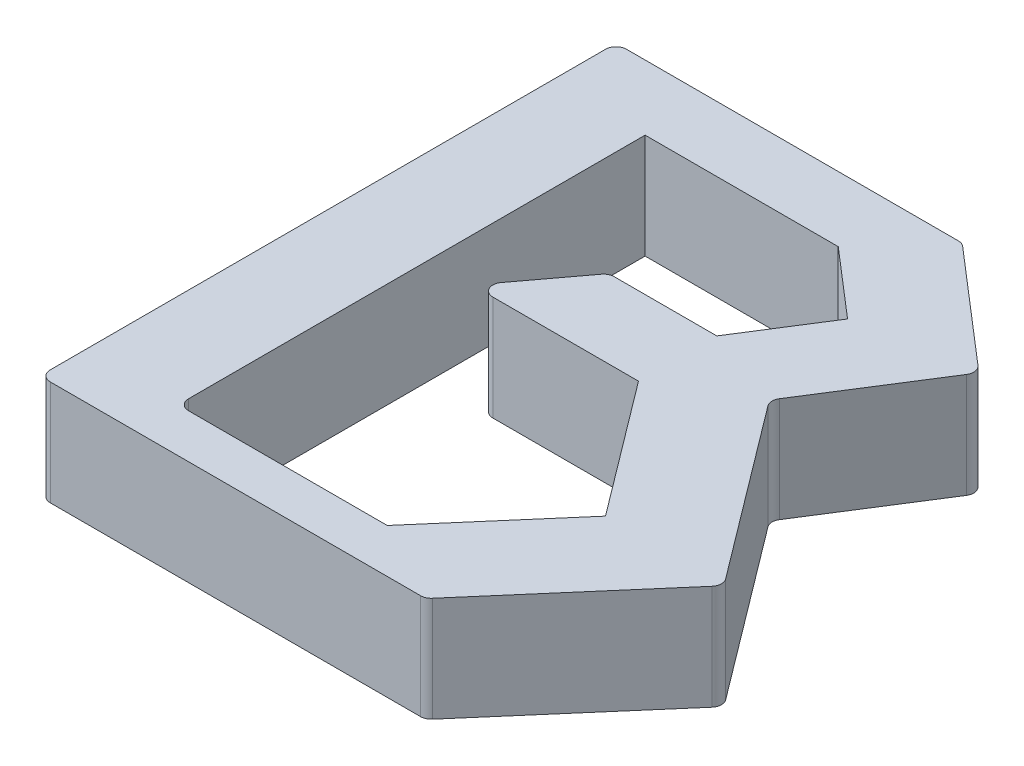
SolidWorks part; units mm, degrees
ref_plane "Front Plane" through (0, 0, 0) normal (0, 0, 1) x (1, 0, 0)
ref_plane "Top Plane" through (0, 0, 0) normal (0, 1, 0) x (1, 0, 0)
ref_plane "Right Plane" through (0, 0, 0) normal (1, 0, 0) x (0, 0, -1)
sketch "Sketch1" plane through (0, 0, 0) normal (0, 1, 0) x (1, 0, 0)
  line L0 (33.0444, 55) -> (44.5679, 45.0706)
  line L1 (0, 0) -> (36.8145, 0)
  line L2 (0, 0) -> (0, 55)
  line L3 (0, 55) -> (33.0444, 55)
  line L6 (44.5679, 45.0706) -> (36.8145, 32.8226)
  line L7 (36.8145, 32.8226) -> (50, 15.3024)
  line L8 (50, 15.3024) -> (36.8145, 0)
  line L9 (8.9879, 48.7885) -> (8.9879, 4.2137)
  line L10 (8.9879, 48.7885) -> (27.4217, 48.7885)
  line L11 (27.4217, 48.7885) -> (33.845, 43.2538)
  line L12 (33.845, 43.2538) -> (29.0072, 35.6117)
  line L13 (29.0072, 35.6117) -> (18.705, 35.6117)
  line L15 (13.1098, 28.136) -> (29.0072, 28.136)
  line L16 (29.0072, 28.136) -> (38.5895, 15.4036)
  line L17 (38.5895, 15.4036) -> (28.9476, 4.2137)
  line L18 (28.9476, 4.2137) -> (8.9879, 4.2137)
  line L19 (13.1098, 28.136) -> (18.705, 35.6117)
  dimension "D1" = 55
extrude "Boss-Extrude1" add sketch "Sketch1" along normal blind 10
fillet "Fillet1" radius 1 10 edges at (44.5679, 5, -45.0706) (36.8145, 5, 0) (50, 5, -15.3024) (13.1098, 5, -28.136) (18.705, 5, -35.6117) (0, 5, 0) (0, 5, -55) (33.0444, 5, -55) (36.8145, 5, -32.8226) (8.9879, 5, -4.2137)
